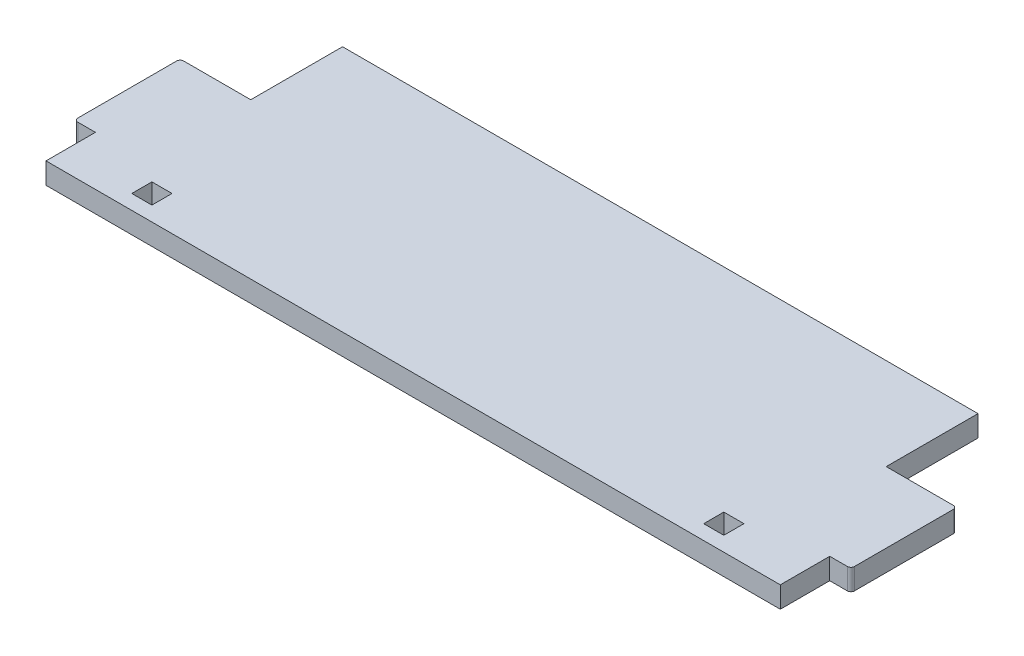
SolidWorks part; units mm, degrees
ref_plane "Спереди" through (0, 0, 0) normal (0, 0, 1) x (1, 0, 0)
ref_plane "Сверху" through (0, 0, 0) normal (0, 1, 0) x (1, 0, 0)
ref_plane "Справа" through (0, 0, 0) normal (1, 0, 0) x (0, 0, -1)
sketch "Эскиз1" plane through (0, 0, 0) normal (0, 1, 0) x (1, 0, 0)
  line L0 (0, 0) -> (0, 1) construction
  line L1 (-52, 0) -> (52, 0)
  line L2 (52, 0) -> (52, 7)
  line L3 (52, 7) -> (55, 7)
  line L4 (55, 7) -> (55, 22)
  line L5 (55, 22) -> (45, 22)
  line L6 (45, 22) -> (45, 35)
  line L7 (45, 35) -> (-45, 35)
  line L8 (-45, 22) -> (-45, 35)
  line L9 (-55, 22) -> (-45, 22)
  line L10 (-55, 7) -> (-55, 22)
  line L11 (-52, 7) -> (-55, 7)
  line L12 (-52, 0) -> (-52, 7)
  line L13 (-39.075, 2.075) -> (-41.925, 4.925) construction
  line L14 (39.075, 4.925) -> (41.925, 4.925)
  line L15 (39.075, 4.925) -> (39.075, 2.075)
  line L16 (39.075, 2.075) -> (41.925, 2.075)
  line L17 (41.925, 4.925) -> (41.925, 2.075)
  line L18 (39.075, 4.925) -> (41.925, 2.075) construction
  line L19 (39.075, 2.075) -> (41.925, 4.925) construction
  line L20 (-39.075, 4.925) -> (-41.925, 2.075) construction
  line L21 (-41.925, 4.925) -> (-41.925, 2.075)
  line L22 (-39.075, 2.075) -> (-41.925, 2.075)
  line L23 (-39.075, 4.925) -> (-39.075, 2.075)
  line L24 (-39.075, 4.925) -> (-41.925, 4.925)
  point P11 (0, 35)
  point P16 (40.5, 3.5)
  point P25 (-40.5, 3.5)
  dimension "D1" = 3
  dimension "D2" = 110
  dimension "D3" = 10
  dimension "D4" = 15
  dimension "D5" = 7
  dimension "D6" = 35
  dimension "D7" = 2.85
  dimension "D9" = 11.5
  dimension "D10" = 3.5
extrude "Бобышка-Вытянуть1" add sketch "Эскиз1" along normal blind 3 contours L24 L23 L1 L15 L14 L17 L2 L3 L4 L5 L6 L7 L8 L9 L10 L11 L12 L21
fillet "Скругление1" radius 0.5 4 edges at (55, 1.5, -22) (55, 1.5, -7) (-55, 1.5, -22) (-55, 1.5, -7)
